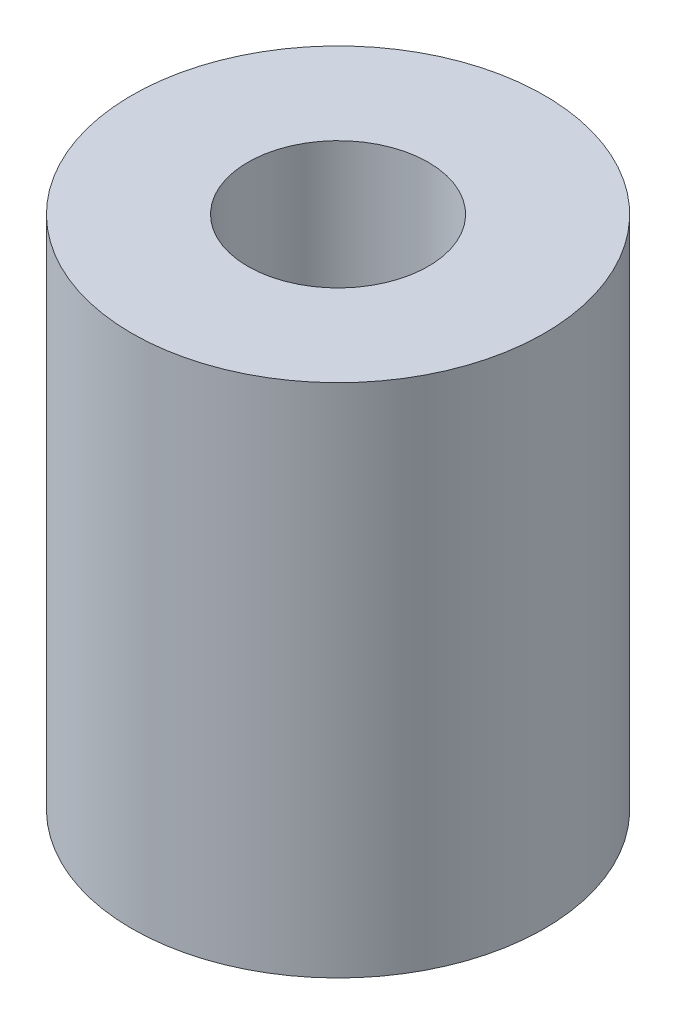
SolidWorks part; units mm, degrees
ref_plane "Спереди" through (0, 0, 0) normal (0, 0, 1) x (1, 0, 0)
ref_plane "Сверху" through (0, 0, 0) normal (0, 1, 0) x (1, 0, 0)
ref_plane "Справа" through (0, 0, 0) normal (1, 0, 0) x (0, 0, -1)
sketch "Эскиз1" plane through (0, 0, 0) normal (0, 1, 0) x (1, 0, 0)
  circle A0 centre (0, 0) radius 4
  circle A1 centre (0, 0) radius 1.75
  dimension "D1" = 3.5
  dimension "D2" = 8
extrude "Бобышка-Вытянуть1" add sketch "Эскиз1" along normal blind 10
